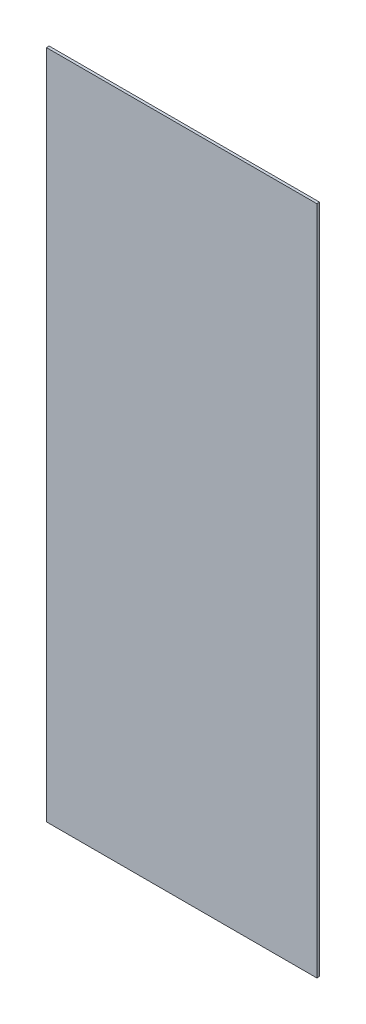
SolidWorks part; units mm, degrees
material "Plain Carbon Steel"
ref_plane "Front Plane" through (0, 0, 0) normal (0, 0, 1) x (1, 0, 0)
ref_plane "Top Plane" through (0, 0, 0) normal (0, 1, 0) x (1, 0, 0)
ref_plane "Right Plane" through (0, 0, 0) normal (1, 0, 0) x (0, 0, -1)
sketch "Sketch1" plane through (0, 0, 0) normal (0, 0, 1) x (1, 0, 0)
  line L1 (100, 248) -> (-100, 248)
  line L2 (100, 248) -> (100, -248)
  line L3 (100, -248) -> (-100, -248)
  line L4 (-100, 248) -> (-100, -248)
  line L5 (100, 248) -> (-100, -248) construction
  line L6 (100, -248) -> (-100, 248) construction
  point P0 (0, 0)
  dimension "D1" = 200
  dimension "D2" = 496
extrude "Boss-Extrude1" add sketch "Sketch1" along normal blind 2
